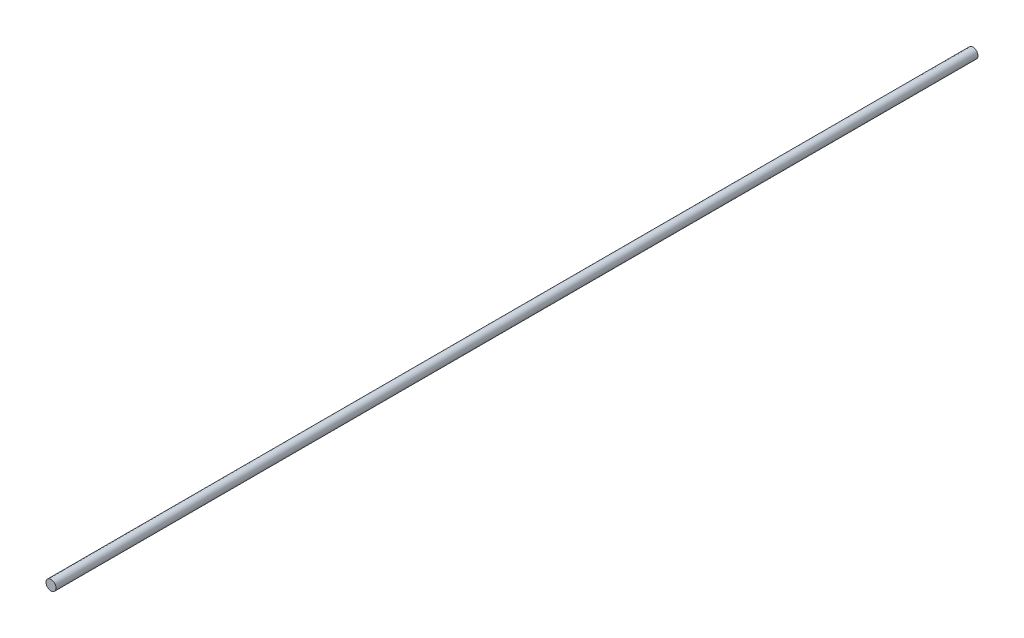
SolidWorks part; units mm, degrees
material "Alloy Steel"
ref_plane "Front Plane" through (0, 0, 0) normal (0, 0, 1) x (1, 0, 0)
ref_plane "Top Plane" through (0, 0, 0) normal (0, 1, 0) x (1, 0, 0)
ref_plane "Right Plane" through (0, 0, 0) normal (1, 0, 0) x (0, 0, -1)
sketch "Sketch1" plane through (0, 0, 0) normal (0, 0, 1) x (1, 0, 0)
  circle A0 centre (0, 0) radius 27.5
  dimension "D1" = 55
extrude "Boss-Extrude1" add sketch "Sketch1" along normal blind 5070
scale "Scale1" bodies to scale 101 scale about centroid uniform scaling yes scale factor 0.1
